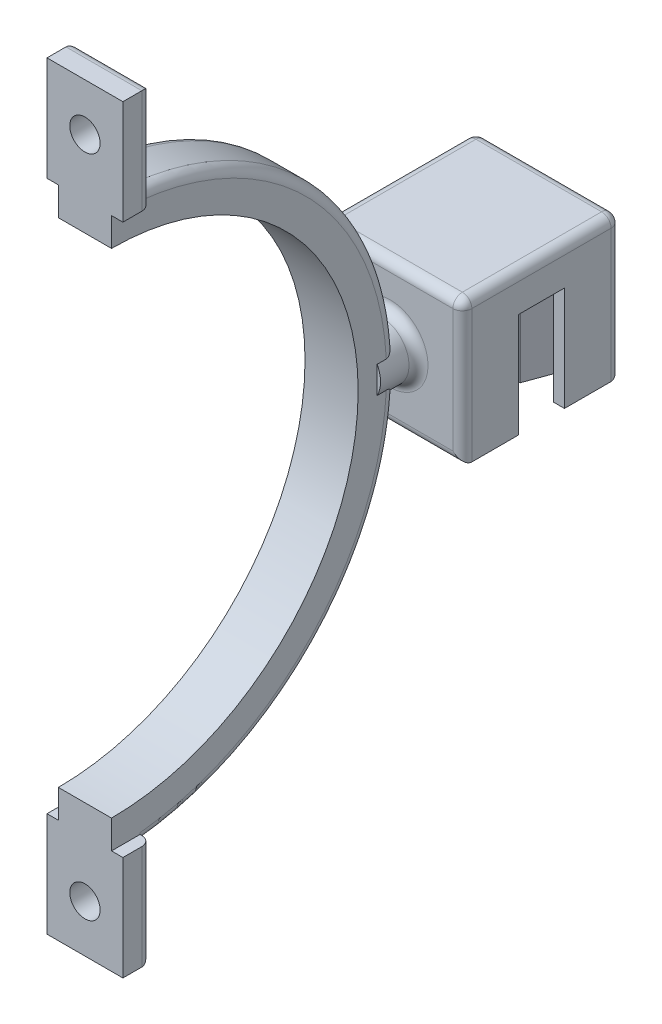
SolidWorks part; units mm, degrees
ref_plane "Front Plane" through (0, 0, 0) normal (0, 0, 1) x (1, 0, 0)
ref_plane "Top Plane" through (0, 0, 0) normal (0, 1, 0) x (1, 0, 0)
ref_plane "Right Plane" through (0, 0, 0) normal (1, 0, 0) x (0, 0, -1)
sketch "Sketch1" plane through (0, 0, 0) normal (0, 1, 0) x (1, 0, 0)
  line L0 (6.5742, -3.3889) -> (7.8835, -3.3889)
  line L1 (5.3458, -6.7639) -> (6.5742, -3.3889)
  line L2 (5.3458, -6.7639) -> (4.3995, -6.7639)
  line L3 (3.1711, -3.3889) -> (4.3995, -6.7639)
  line L4 (1.8618, -3.3889) -> (3.1711, -3.3889)
  line L5 (-7.563, -3.3889) -> (-6.2537, -3.3889)
  line L6 (-4.079, -6.7639) -> (-5.0253, -6.7639)
  line L7 (-6.2537, -3.3889) -> (-5.0253, -6.7639)
  line L8 (-4.079, -6.7639) -> (-2.8506, -3.3889)
  line L9 (-2.8506, -3.3889) -> (-1.5413, -3.3889)
  line L10 (0.6334, -6.7639) -> (1.8618, -3.3889)
  line L11 (0.6334, -6.7639) -> (-0.3129, -6.7639)
  line L12 (-1.5413, -3.3889) -> (-0.3129, -6.7639)
  line L13 (6.5742, 1.2611) -> (7.8835, 1.2611)
  line L14 (5.3458, 4.6361) -> (6.5742, 1.2611)
  line L15 (5.3458, 4.6361) -> (4.3995, 4.6361)
  line L16 (3.1711, 1.2611) -> (4.3995, 4.6361)
  line L17 (1.8618, 1.2611) -> (3.1711, 1.2611)
  line L18 (0.6334, 4.6361) -> (1.8618, 1.2611)
  line L19 (0.6334, 4.6361) -> (-0.3129, 4.6361)
  line L20 (-1.5413, 1.2611) -> (-0.3129, 4.6361)
  line L21 (-2.8506, 1.2611) -> (-1.5413, 1.2611)
  line L22 (-4.079, 4.6361) -> (-2.8506, 1.2611)
  line L23 (-4.079, 4.6361) -> (-5.0253, 4.6361)
  line L24 (-6.2537, 1.2611) -> (-5.0253, 4.6361)
  line L25 (-7.563, 1.2611) -> (-6.2537, 1.2611)
  line L26 (-7.563, -3.3889) -> (-7.563, -9.4027)
  line L27 (-7.563, -9.4027) -> (7.8835, -9.4027)
  line L28 (7.8835, -9.4027) -> (7.8835, -3.3889)
  line L29 (7.8835, 1.2611) -> (7.8835, 7.2749)
  line L30 (7.8835, 7.2749) -> (-7.563, 7.2749)
  line L31 (-7.563, 7.2749) -> (-7.563, 1.2611)
extrude "Boss-Extrude1" add sketch "Sketch1" along normal blind 11
sketch "Sketch2" plane through (0, 11, 0) normal (0, 1, 0) x (1, 0, 0)
  line L0 (-7.563, 7.2749) -> (-7.563, 1.2611) construction
  line L1 (7.8835, -9.4027) -> (-7.563, -9.4027)
  line L2 (7.8835, -9.4027) -> (7.8835, 7.2749)
  line L3 (7.8835, 7.2749) -> (-7.563, 7.2749)
  line L4 (-7.563, -9.4027) -> (-7.563, 7.2749)
extrude "Boss-Extrude2" add sketch "Sketch2" along normal blind 4
sketch "Sketch3" plane through (0, 0, 9.4027) normal (0, 0, 1) x (1, 0, 0)
  line L0 (0.1603, 0) -> (0.1603, 15) construction
  line L1 (-7.563, 0) -> (7.8835, 0) construction
  line L2 (-7.563, 15) -> (7.8835, 15) construction
  line L3 (-7.563, 7.5) -> (7.8835, 7.5) construction
  line L4 (-7.563, 15) -> (-7.563, 0) construction
  line L5 (7.8835, 15) -> (7.8835, 0) construction
  circle A0 centre (0.1603, 7.5) radius 3
  dimension "D1" = 6
extrude "Boss-Extrude3" add sketch "Sketch3" along normal blind 4
sketch "Sketch7" plane through (0, 0, 0) normal (1, 0, 0) x (0, 0, -1)
  line L0 (-41.4027, 33.5) -> (-41.4027, 41.5783) construction
  line L1 (-21.7166, 7.5) -> (-76.3268, 7.5) construction
  line L2 (-9.4027, 15) -> (-9.4027, 0) construction
  line L3 (-41.4027, -22.5) -> (-41.4027, -18.5)
  line L4 (-41.4027, 33.5) -> (-41.4027, 37.5)
  arc A0 (-41.4027, -22.5) -> (-41.4027, 37.5) centre (-41.4027, 7.5) ccw
  arc A1 (-41.4027, -18.5) -> (-41.4027, 33.5) centre (-41.4027, 7.5) ccw
  point P6 (-9.4027, 7.5)
  dimension "D2" = 60
  dimension "D3" = 52
  dimension "D1" = 32
extrude "Boss-Extrude4" add sketch "Sketch7" along normal mid plane 5.6
sketch "Sketch9" plane through (0, 0, 0) normal (0, -1, 0) x (-1, 0, 0)
  line L0 (7.463, -9.4027) -> (7.463, -3.4889)
  line L1 (7.563, -9.4027) -> (-7.8835, -9.4027) construction
  line L2 (7.463, -3.4889) -> (6.3237, -3.4889)
  line L3 (6.3237, -3.4889) -> (5.0953, -6.8639)
  line L4 (5.0953, -6.8639) -> (4.009, -6.8639)
  line L5 (4.009, -6.8639) -> (2.7806, -3.4889)
  line L6 (2.7806, -3.4889) -> (1.6113, -3.4889)
  line L7 (1.6113, -3.4889) -> (0.3829, -6.8639)
  line L8 (0.3829, -6.8639) -> (-0.7034, -6.8639)
  line L9 (-0.7034, -6.8639) -> (-1.9318, -3.4889)
  line L10 (-1.9318, -3.4889) -> (-3.1011, -3.4889)
  line L11 (-3.1011, -3.4889) -> (-4.3295, -6.8639)
  line L12 (-4.3295, -6.8639) -> (-5.4158, -6.8639)
  line L13 (-5.4158, -6.8639) -> (-6.6442, -3.4889)
  line L14 (-6.6442, -3.4889) -> (-7.7835, -3.4889)
  line L15 (-7.7835, -3.4889) -> (-7.7835, -9.4027)
  line L16 (-7.7835, -9.4027) -> (-7.8835, -9.4027)
  line L17 (-7.8835, -9.4027) -> (-7.8835, -3.3889)
  line L18 (-7.8835, -3.3889) -> (-6.5742, -3.3889)
  line L19 (-6.5742, -3.3889) -> (-5.3458, -6.7639) construction
  line L20 (-7.8835, -3.3889) -> (-6.5742, -3.3889) construction
  line L21 (-6.5742, -3.3889) -> (-5.3458, -6.7639)
  line L22 (-5.3458, -6.7639) -> (-4.3995, -6.7639)
  line L23 (-4.3995, -6.7639) -> (-3.1711, -3.3889)
  line L24 (-4.3995, -6.7639) -> (-3.1711, -3.3889) construction
  line L25 (-3.1711, -3.3889) -> (-1.8618, -3.3889) construction
  line L26 (-3.1711, -3.3889) -> (-1.8618, -3.3889)
  line L27 (-1.8618, -3.3889) -> (-0.6334, -6.7639)
  line L28 (-1.8618, -3.3889) -> (-0.6334, -6.7639) construction
  line L29 (-0.6334, -6.7639) -> (0.3129, -6.7639)
  line L30 (0.3129, -6.7639) -> (1.5413, -3.3889)
  line L31 (1.5413, -3.3889) -> (2.8506, -3.3889) construction
  line L32 (0.3129, -6.7639) -> (1.5413, -3.3889) construction
  line L33 (1.5413, -3.3889) -> (2.8506, -3.3889)
  line L34 (2.8506, -3.3889) -> (4.079, -6.7639)
  line L35 (2.8506, -3.3889) -> (4.079, -6.7639) construction
  line L36 (4.079, -6.7639) -> (5.0253, -6.7639)
  line L37 (5.0253, -6.7639) -> (6.2537, -3.3889)
  line L38 (5.0253, -6.7639) -> (6.2537, -3.3889) construction
  line L39 (6.2537, -3.3889) -> (7.563, -3.3889)
  line L40 (7.563, -3.3889) -> (7.563, -9.4027)
  line L41 (7.563, -9.4027) -> (7.463, -9.4027)
  line L42 (6.2537, -3.3889) -> (6.2537, 1.2611) construction
  line L43 (6.2537, -1.0639) -> (-9.1214, -1.0639) construction
  line L44 (7.563, 1.2611) -> (7.563, 7.2749)
  line L45 (6.2537, 1.2611) -> (7.563, 1.2611)
  line L46 (5.0253, 4.6361) -> (6.2537, 1.2611)
  line L47 (4.079, 4.6361) -> (5.0253, 4.6361)
  line L48 (2.8506, 1.2611) -> (4.079, 4.6361)
  line L49 (1.5413, 1.2611) -> (2.8506, 1.2611)
  line L50 (0.3129, 4.6361) -> (1.5413, 1.2611)
  line L51 (-0.6334, 4.6361) -> (0.3129, 4.6361)
  line L52 (-1.8618, 1.2611) -> (-0.6334, 4.6361)
  line L53 (-3.1711, 1.2611) -> (-1.8618, 1.2611)
  line L54 (-4.3995, 4.6361) -> (-3.1711, 1.2611)
  line L55 (-5.3458, 4.6361) -> (-4.3995, 4.6361)
  line L56 (-6.5742, 1.2611) -> (-5.3458, 4.6361)
  line L57 (-7.8835, 1.2611) -> (-6.5742, 1.2611)
  line L58 (-7.8835, 7.2749) -> (-7.8835, 1.2611)
  line L59 (-7.7835, 7.2749) -> (-7.8835, 7.2749)
  line L60 (-7.7835, 1.3611) -> (-7.7835, 7.2749)
  line L61 (-6.6442, 1.3611) -> (-7.7835, 1.3611)
  line L62 (-5.4158, 4.7361) -> (-6.6442, 1.3611)
  line L63 (-4.3295, 4.7361) -> (-5.4158, 4.7361)
  line L64 (-3.1011, 1.3611) -> (-4.3295, 4.7361)
  line L65 (-1.9318, 1.3611) -> (-3.1011, 1.3611)
  line L66 (-0.7034, 4.7361) -> (-1.9318, 1.3611)
  line L67 (0.3829, 4.7361) -> (-0.7034, 4.7361)
  line L68 (1.6113, 1.3611) -> (0.3829, 4.7361)
  line L69 (2.7806, 1.3611) -> (1.6113, 1.3611)
  line L70 (4.009, 4.7361) -> (2.7806, 1.3611)
  line L71 (5.0953, 4.7361) -> (4.009, 4.7361)
  line L72 (6.3237, 1.3611) -> (5.0953, 4.7361)
  line L73 (7.463, 1.3611) -> (6.3237, 1.3611)
  line L74 (7.463, 7.2749) -> (7.463, 1.3611)
  line L75 (7.563, 7.2749) -> (7.463, 7.2749)
  point P99 (6.9083, -3.3889)
  point P100 (-6.03, -5.1764)
  dimension "D1" = 0.1
  dimension "D2" = 0.1
  dimension "D3" = 0.1
  dimension "D4" = 0.1
  dimension "D5" = 0.1
  dimension "D6" = 0.1
  dimension "D7" = 0.1
  dimension "D8" = 0.1
  dimension "D9" = 0.1
  dimension "D10" = 0.1
extrude "Cut-Extrude1" cut sketch "Sketch9" against normal blind 11
sketch "Sketch11" plane through (0, 11, 0) normal (0, -1, 0) x (1, 0, 0)
  line L1 (7.7835, 9.4027) -> (7.8835, 9.4027)
  line L2 (7.7835, 9.4027) -> (7.7835, -7.2749)
  line L3 (7.7835, -7.2749) -> (7.8835, -7.2749)
  line L4 (7.8835, 9.4027) -> (7.8835, -7.2749)
  line L5 (-7.563, 9.4027) -> (-7.463, 9.4027)
  line L6 (-7.563, 9.4027) -> (-7.563, -7.2749)
  line L7 (-7.563, -7.2749) -> (-7.463, -7.2749)
  line L8 (-7.463, 9.4027) -> (-7.463, -7.2749)
extrude "Cut-Extrude2" cut sketch "Sketch11" against normal blind 11
ref_plane "Plane1" through (0, -22, 0) normal (0, -1, 0) x (-1, 0, 0)
sketch "Sketch12" plane through (0, 0, 41.4027) normal (0, 0, 1) x (1, 0, 0)
  line L0 (2.8, -18.5) -> (-2.8, -18.5) construction
  line L1 (4, -18.5) -> (-4, -18.5)
  line L2 (4, -18.5) -> (4, -32.5)
  line L3 (4, -32.5) -> (-4, -32.5)
  line L4 (-4, -18.5) -> (-4, -32.5)
  circle A0 centre (0, -27.5) radius 1.6
  point P5 (0, 0)
  point P6 (0, -32.5)
  point P9 (0, -18.5)
  point P10 (0, -18.5)
  dimension "D3" = 3.2
  dimension "D1" = 14
  dimension "D2" = 8
  dimension "D4" = 5
ref_plane "Plane2" through (0, 7.5, 0) normal (0, 1, 0) x (1, 0, 0)
extrude "Boss-Extrude5" add sketch "Sketch12" against normal blind 3
mirror "Mirror1" about plane through (0, 7.5, 0) normal (0, 1, 0) of "Boss-Extrude5"
fillet "Fillet1" radius 1 21 edges at (0.1603, 0, 9.4027) (-7.463, 7.5, 9.4027) (7.7835, 7.5, 9.4027) (3.1603, 7.5, 9.4027) (-7.463, 7.5, -7.2749) (0.1603, 0, -7.2749) (7.7835, 7.5, -7.2749) (0.1603, 15, 9.4027) (-7.463, 15, 1.0639) (0.1603, 15, -7.2749) (7.7835, 15, 1.0639) (0, -32.5, 38.4027) (-4, -25.5, 38.4027) (4, -25.5, 38.4027) (0, 47.5, 38.4027) (4, 40.5, 38.4027) (-4, 40.5, 38.4027) (-2.8, 27.8044, 19.318) (2.8, 28.1476, 19.6386) (-2.8, -12.8044, 19.318) (2.8, -13.1476, 19.6386)
sketch "Sketch14" plane through (0, 33.5, 0) normal (0, -1, 0) x (1, 0, 0)
  line L1 (-2.8, 41.4027) -> (-4.2655, 41.4027)
  line L2 (-2.8, 41.4027) -> (-2.8, 38.0829)
  line L3 (-2.8, 38.0829) -> (-4.2655, 38.0829)
  line L4 (-4.2655, 41.4027) -> (-4.2655, 38.0829)
  line L5 (2.8, 41.4027) -> (4.3797, 41.4027)
  line L6 (2.8, 41.4027) -> (2.8, 38.0829)
  line L7 (2.8, 38.0829) -> (4.3797, 38.0829)
  line L8 (4.3797, 41.4027) -> (4.3797, 38.0829)
extrude "Cut-Extrude3" cut sketch "Sketch14" against normal blind 3
sketch "Sketch15" plane through (0, -18.5, 0) normal (0, 1, 0) x (1, 0, 0)
  line L1 (2.8, -41.4027) -> (4.3071, -41.4027)
  line L2 (2.8, -41.4027) -> (2.8, -37.686)
  line L3 (2.8, -37.686) -> (4.3071, -37.686)
  line L4 (4.3071, -41.4027) -> (4.3071, -37.686)
  line L5 (-2.8, -41.4027) -> (-4.3548, -41.4027)
  line L6 (-2.8, -41.4027) -> (-2.8, -37.9589)
  line L7 (-2.8, -37.9589) -> (-4.3548, -37.9589)
  line L8 (-4.3548, -41.4027) -> (-4.3548, -37.9589)
extrude "Cut-Extrude4" cut sketch "Sketch15" against normal blind 3
ref_plane "Plane3" through (0, 0, 51.4027) normal (0, 0, 1) x (1, 0, 0)
